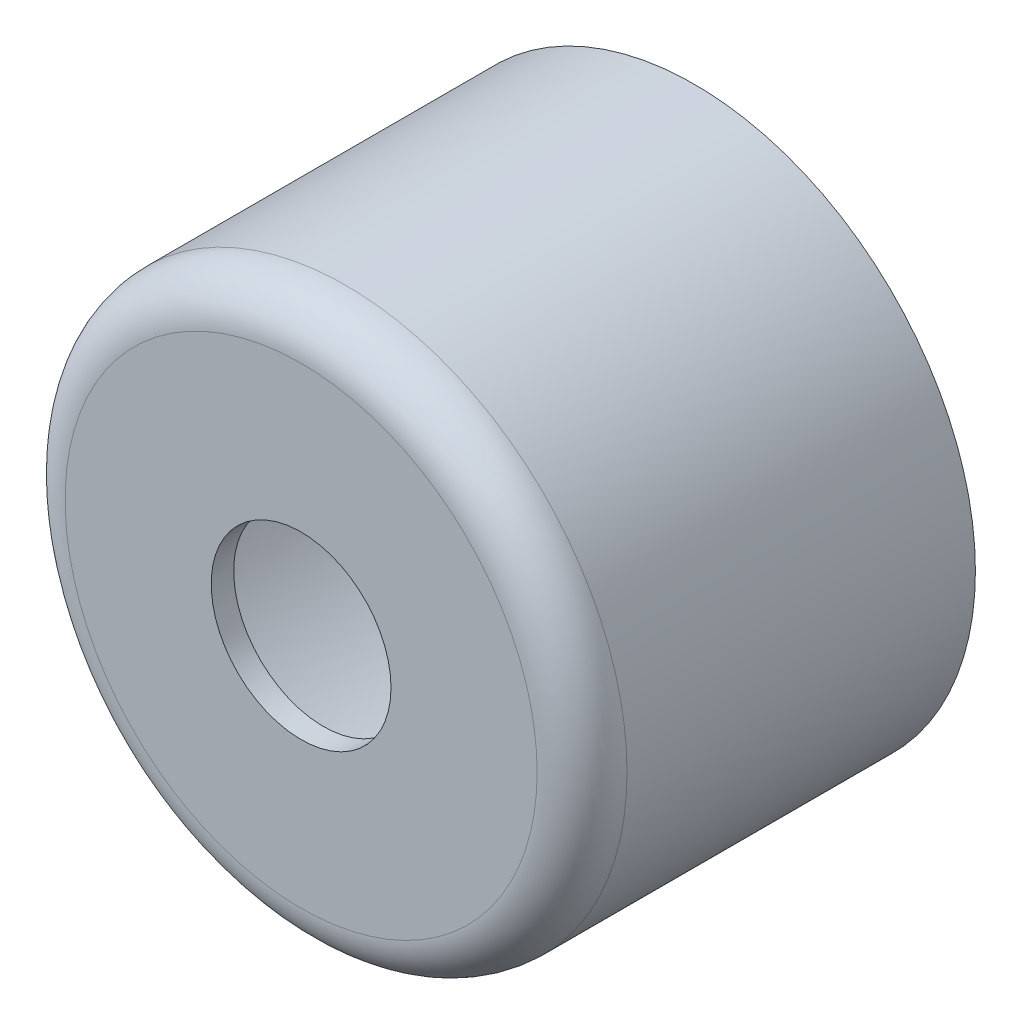
SolidWorks part; units mm, degrees
ref_plane "Front Plane" through (0, 0, 0) normal (0, 0, 1) x (1, 0, 0)
ref_plane "Top Plane" through (0, 0, 0) normal (0, 1, 0) x (1, 0, 0)
ref_plane "Right Plane" through (0, 0, 0) normal (1, 0, 0) x (0, 0, -1)
ref_plane "Plane2" through (0, 0, -33.1) normal (0, 0, 1) x (1, 0, 0)
sheet metal parameters "Sheet-Metal2" thickness 0.9 parameters "D1"=0.5
sketch "Sketch8" plane through (0, 0, 0) normal (0, 0, 1) x (1, 0, 0)
  circle A0 centre (0, 0) radius 12.5
  dimension "D1" = 25
extrude "Extrude6" add sketch "Sketch8" along normal blind 17.5 separate body
fillet "Fillet2" radius 2 1 edges at (12.5, 0, 17.5)
shell "Shell1" thickness 1
sketch "Sketch9" plane through (0, 0, 17.5) normal (0, 0, 1) x (1, 0, 0)
  circle A0 centre (0, 0) radius 4
extrude "Extrude7" cut sketch "Sketch9" against normal through all
